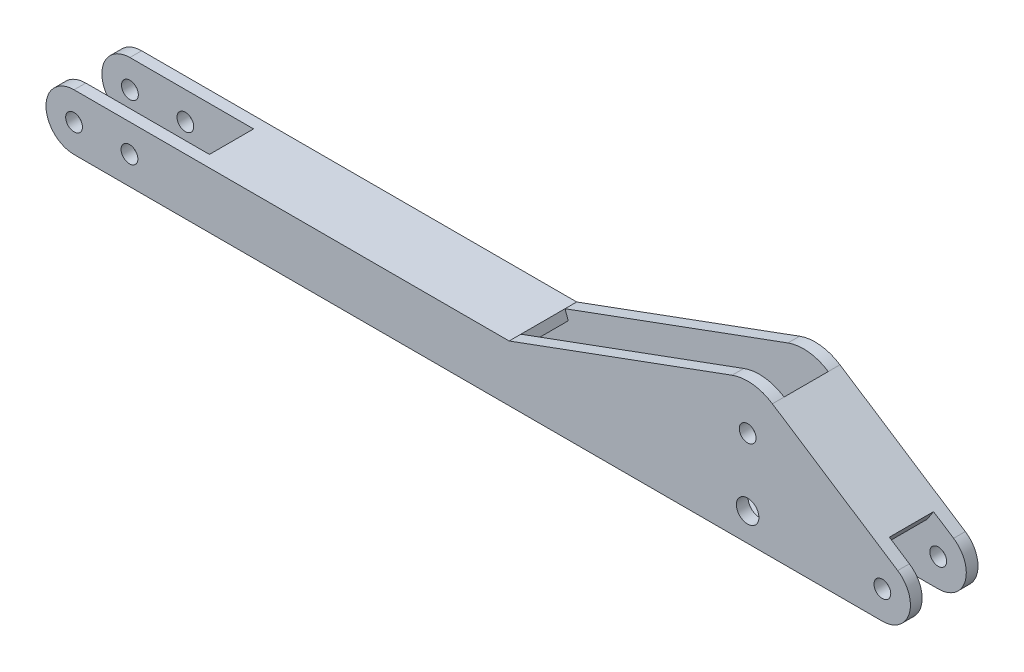
SolidWorks part; units mm, degrees
ref_plane "Front Plane" through (0, 0, 0) normal (0, 0, 1) x (1, 0, 0)
ref_plane "Top Plane" through (0, 0, 0) normal (0, 1, 0) x (1, 0, 0)
ref_plane "Right Plane" through (0, 0, 0) normal (1, 0, 0) x (0, 0, -1)
sketch "Sketch1" plane through (0, 0, 0) normal (0, 0, 1) x (1, 0, 0)
  line L0 (0, 0) -> (3660, 0) construction
  line L2 (0, 127) -> (1970, 127)
  line L3 (1970, 127) -> (2979.3696, 497.4483)
  line L4 (3162.0477, 476.6692) -> (3729.4149, 106.3512)
  line L5 (3660, -127) -> (0, -127)
  circle A0 centre (0, 0) radius 38
  arc A1 (0, 127) -> (0, -127) centre (0, 0) ccw
  circle A2 centre (3660, 0) radius 38
  arc A3 (3660, -127) -> (3729.4149, 106.3512) centre (3660, 0) ccw
  circle A4 centre (3050, 0) radius 51
  circle A5 centre (3050, 305) radius 38
  arc A6 (3162.0477, 476.6692) -> (2979.3696, 497.4483) centre (3050, 305) ccw
  circle A7 centre (251, 0) radius 38
  point P17 (3050, 549.8022)
  dimension "D1" = 254
  dimension "D2" = 76
  dimension "D6" = 102
  dimension "D7" = 205
  dimension "D9" = 76
  dimension "D3" = 3050
  dimension "D4" = 610
  dimension "D5" = 305
  dimension "D8" = 1970
  dimension "D10" = 251
extrude "Boss-Extrude1" add sketch "Sketch1" along normal blind 306
sketch "Sketch2" plane through (0, 127, 0) normal (0, 1, 0) x (1, 0, 0)
  line L0 (0, -153) -> (919.7835, -153) construction
  line L1 (0, -306) -> (0, 0) construction
  line L2 (-127, 0) -> (-127, -306) construction
  line L3 (-127, -53) -> (560, -53)
  line L4 (-127, -53) -> (-127, -253)
  line L5 (-127, -253) -> (560, -253)
  line L6 (560, -53) -> (560, -253)
  line L7 (1970, -306) -> (1970, 0) construction
  dimension "D1" = 200
  dimension "D2" = 1410
extrude "Cut-Extrude1" cut sketch "Sketch2" against normal blind 214
sketch "Sketch3" plane through (0, 0, 306) normal (0, 0, 1) x (1, 0, 0)
  line L0 (3729.4149, 106.3512) -> (3638.66, 165.5865)
  line L1 (3729.4149, 106.3512) -> (3162.0477, 476.6692) construction
  line L2 (3638.66, 165.5865) -> (3447.6901, -127)
  line L3 (0, -127) -> (3660, -127) construction
  line L4 (3447.6901, -127) -> (3660, -127)
  arc A0 (3660, -127) -> (3729.4149, 106.3512) centre (3660, 0) ccw construction
  circle A1 centre (3660, 0) radius 38 construction
  arc A2 (3660, -127) -> (3729.4149, 106.3512) centre (3660, 0) ccw
  circle A3 centre (3660, 0) radius 38
  dimension "D1" = 21.34
extrude "Cut-Extrude2" cut sketch "Sketch3" against normal blind 200 from offset 53 offset against normal yes
sketch "Sketch4" plane through (560, 0, 0) normal (-1, 0, 0) x (0, 0, 1)
  line L1 (53, -87) -> (53, 127) construction
  line L2 (253, -87) -> (53, -87)
  line L3 (253, -87) -> (253, 87)
  line L4 (253, 87) -> (53, 87)
  line L5 (53, -87) -> (53, 87)
  line L6 (306, 127) -> (0, 127) construction
  dimension "D1" = 40
extrude "Cut-Extrude3" cut sketch "Sketch4" against normal blind 2690
sketch "Sketch5" plane through (192.7749, -525.2586, 0) normal (-0.3445, 0.9388, 0) x (0.9388, 0.3445, 0)
  line L0 (1893.1377, -153) -> (2968.3395, -153) construction
  line L1 (1893.1377, -306) -> (1893.1377, 0) construction
  line L2 (2968.3395, -306) -> (2968.3395, 0) construction
  line L4 (1893.1377, -253) -> (3132.6777, -253)
  line L5 (1893.1377, -253) -> (1893.1377, -53)
  line L6 (1893.1377, -53) -> (3132.6777, -53)
  line L7 (3132.6777, -253) -> (3132.6777, -53)
  dimension "D1" = 53
  dimension "D2" = 1239.54
extrude "Cut-Extrude4" cut sketch "Sketch5" against normal up to surface (227.9573 mm away)
sketch "Sketch6" plane through (2475.8444, -1615.9725, 0) normal (0.8374, -0.5466, 0) x (0, 0, -1)
  line L0 (-253, 2127.4615) -> (-253, 1778.0673) construction
  line L1 (-53, 1778.0673) -> (-253, 1778.0673)
  line L2 (-53, 1778.0673) -> (-53, 2074.4615)
  line L3 (-53, 2074.4615) -> (-253, 2074.4615)
  line L4 (-253, 1778.0673) -> (-253, 2074.4615)
  line L6 (-53, 2127.4615) -> (-253, 2127.4615) construction
  dimension "D1" = 53
extrude "Cut-Extrude5" cut sketch "Sketch6" against normal blind 2690
